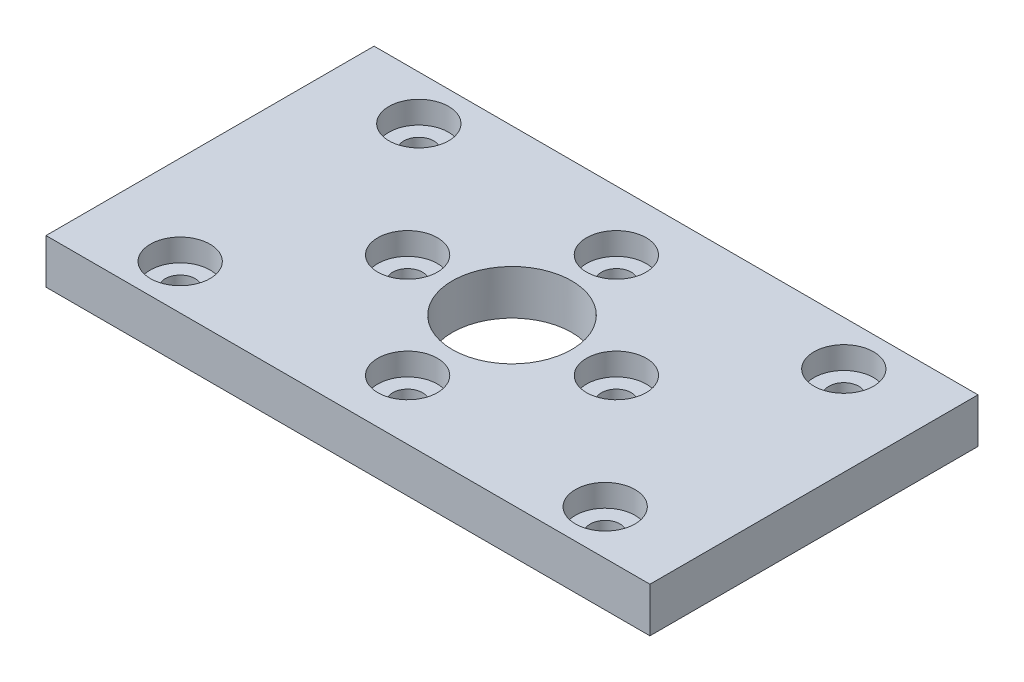
SolidWorks part; units mm, degrees
ref_plane "Front Plane" through (0, 0, 0) normal (0, 0, 1) x (1, 0, 0)
ref_plane "Top Plane" through (0, 0, 0) normal (0, 1, 0) x (1, 0, 0)
ref_plane "Right Plane" through (0, 0, 0) normal (1, 0, 0) x (0, 0, -1)
sketch "Sketch1" plane through (0, 0, 0) normal (0, 1, 0) x (1, 0, 0)
  line L1 (-20.25, -11) -> (20.25, -11)
  line L2 (-20.25, -11) -> (-20.25, 11)
  line L3 (-20.25, 11) -> (20.25, 11)
  line L4 (20.25, -11) -> (20.25, 11)
  line L5 (-20.25, -11) -> (20.25, 11) construction
  line L6 (-20.25, 11) -> (20.25, -11) construction
  point P0 (0, 0)
  dimension "D1" = 40.5
  dimension "D2" = 22
extrude "Boss-Extrude1" add sketch "Sketch1" along normal blind 3
sketch "Sketch2" plane through (0, 3, 0) normal (0, 1, 0) x (1, 0, 0)
  line L0 (-20.25, 11) -> (-20.25, -11) construction
  line L1 (20.25, -11) -> (20.25, 11) construction
  line L2 (20.25, 11) -> (-20.25, 11) construction
  line L3 (-20.25, -11) -> (20.25, -11) construction
  circle A0 centre (-14.25, 8) radius 1
  circle A1 centre (-14.25, -8) radius 1
  circle A2 centre (14.25, -8) radius 1
  circle A3 centre (14.25, 8) radius 1
  dimension "D9" = 2
  dimension "D10" = 2
  dimension "D11" = 2
  dimension "D12" = 2
  dimension "D1" = 6
  dimension "D2" = 6
  dimension "D3" = 6
  dimension "D4" = 6
  dimension "D5" = 3
  dimension "D6" = 3
  dimension "D7" = 3
  dimension "D8" = 3
extrude "Cut-Extrude1" cut sketch "Sketch2" against normal blind 10
sketch "Sketch3" plane through (0, 3, 0) normal (0, 1, 0) x (1, 0, 0)
  circle A0 centre (0, 0) radius 4
  dimension "D1" = 8
extrude "Cut-Extrude2" cut sketch "Sketch3" against normal blind 10
sketch "Sketch4" plane through (0, 3, 0) normal (0, 1, 0) x (1, 0, 0)
  circle A0 centre (0, 0) radius 7 construction
  circle A1 centre (0, 7) radius 1
  circle A2 centre (7, 0) radius 1
  circle A3 centre (0, -7) radius 1
  circle A4 centre (-7, 0) radius 1
  point P14 (0, 0)
  dimension "D1" = 14
  dimension "D2" = 2
  dimension "D3" = 4
extrude "Cut-Extrude3" cut sketch "Sketch4" against normal blind 10
sketch "Sketch5" plane through (0, 3, 0) normal (0, 1, 0) x (1, 0, 0)
  line L0 (-26.3744, 0) -> (24.612, 0) construction
  circle A0 centre (14.25, 8) radius 2
  circle A1 centre (0, 7) radius 2
  circle A2 centre (-14.25, 8) radius 2
  circle A3 centre (7, 0) radius 2
  circle A4 centre (-7, 0) radius 2
  circle A5 centre (-14.25, -8) radius 2
  circle A6 centre (0, -7) radius 2
  circle A7 centre (14.25, -8) radius 2
  dimension "D1" = 4
  dimension "D2" = 4
  dimension "D3" = 4
  dimension "D4" = 4
  dimension "D5" = 4
extrude "Cut-Extrude4" cut sketch "Sketch5" against normal blind 1.5
